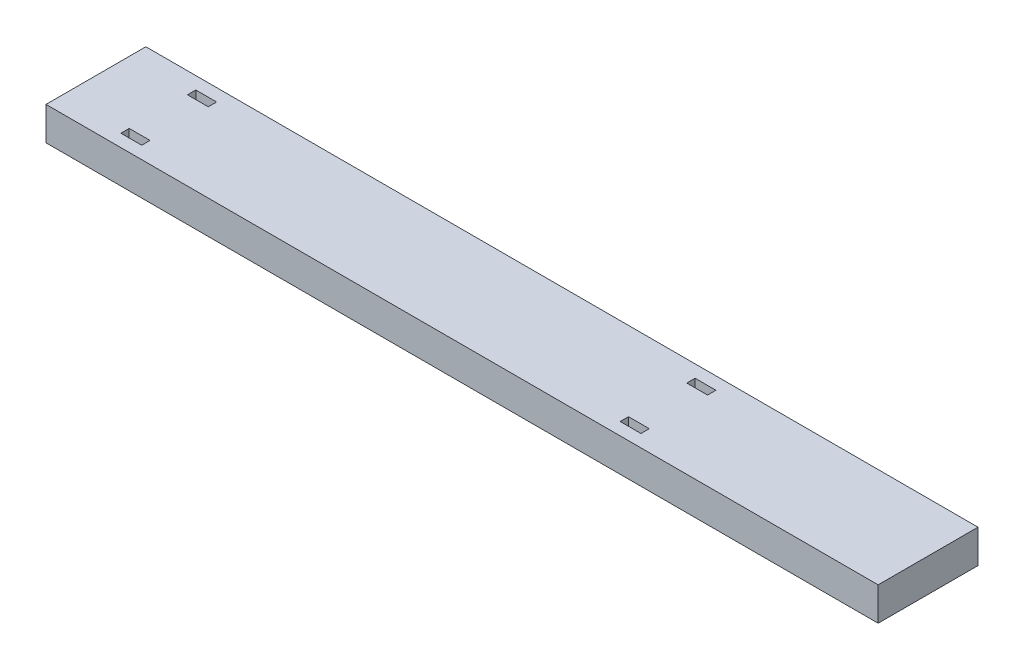
SolidWorks part; units mm, degrees
ref_plane "前视基准面" through (0, 0, 0) normal (0, 0, 1) x (1, 0, 0)
ref_plane "上视基准面" through (0, 0, 0) normal (0, 1, 0) x (1, 0, 0)
ref_plane "右视基准面" through (0, 0, 0) normal (1, 0, 0) x (0, 0, -1)
sketch "Sketch1" plane through (0, 0, 0) normal (0, 1, 0) x (1, 0, 0)
  line L0 (0, 0) -> (0, 24)
  line L1 (0, 24) -> (200, 24)
  line L2 (200, 24) -> (200, 0)
  line L3 (200, 0) -> (0, 0)
  dimension "D1" = 24
  dimension "D2" = 200
extrude "Boss-Extrude2" add sketch "Sketch1" along normal blind 8
sketch "Sketch2" plane through (0, 8, 0) normal (0, 1, 0) x (1, 0, 0)
  line L0 (15, 21) -> (15, 19)
  line L1 (15, 19) -> (20, 19)
  line L2 (20, 19) -> (20, 21)
  line L3 (20, 21) -> (15, 21)
  line L4 (135, 21) -> (135, 19)
  line L5 (135, 19) -> (140, 19)
  line L6 (140, 19) -> (140, 21)
  line L7 (140, 21) -> (135, 21)
  line L8 (0, 24) -> (0, 0) construction
  line L9 (200, 24) -> (0, 24) construction
  line L10 (0, 0) -> (200, 0) construction
  line L11 (0, 0) -> (200, 0) construction
  line L12 (140, 5) -> (140, 3)
  line L13 (135, 5) -> (140, 5)
  line L14 (140, 3) -> (135, 3)
  line L15 (135, 3) -> (135, 5)
  line L16 (15, 5) -> (20, 5)
  line L17 (15, 3) -> (15, 5)
  line L18 (20, 3) -> (15, 3)
  line L19 (20, 5) -> (20, 3)
  line L20 (200, 0) -> (200, 24) construction
  point P15 (0, 0)
  point P27 (0, 0)
  dimension "D1" = 15
  dimension "D2" = 3
  dimension "D3" = 2
  dimension "D4" = 5
  dimension "D5" = 5
  dimension "D6" = 135
  dimension "D7" = 15
  dimension "D8" = 3
  dimension "D9" = 2
  dimension "D10" = 5
  dimension "D11" = 3
  dimension "D12" = 5
  dimension "D13" = 60
  dimension "D14" = 2
extrude "Cut-Extrude1" cut sketch "Sketch2" against normal through all
